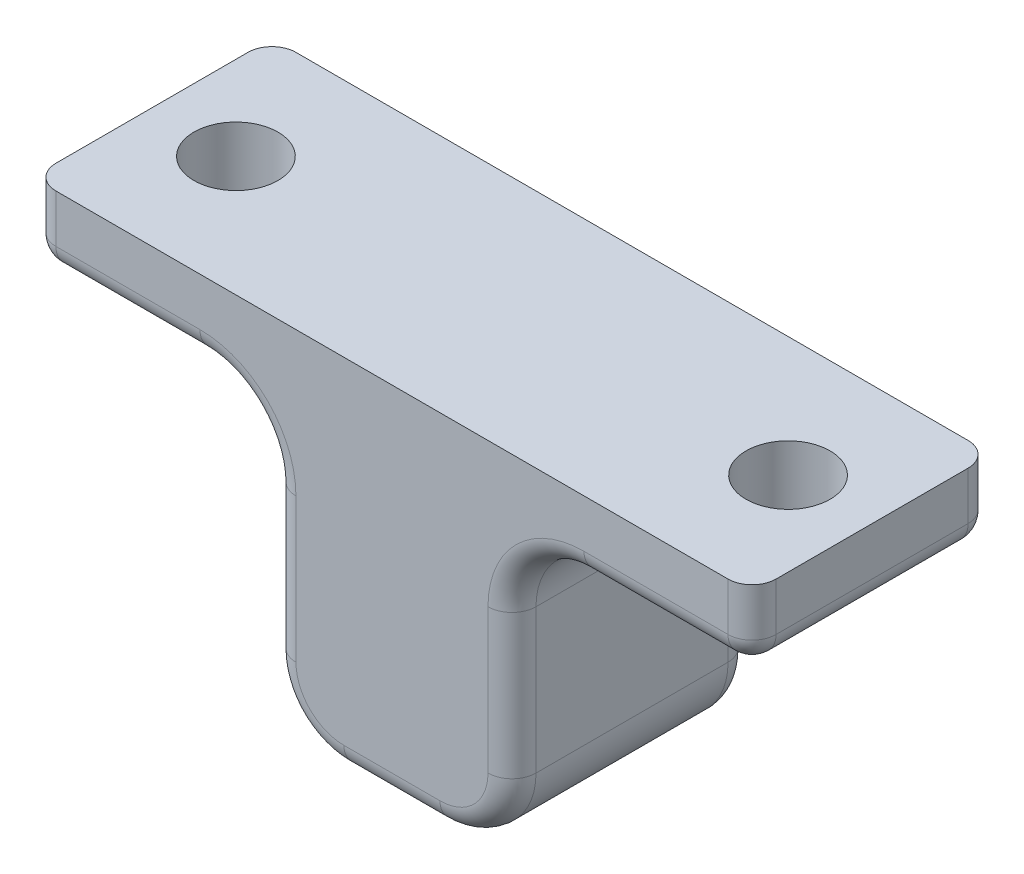
SolidWorks part; units mm, degrees
ref_plane "正面" through (0, 0, 0) normal (0, 0, 1) x (1, 0, 0)
ref_plane "平面" through (0, 0, 0) normal (0, 1, 0) x (1, 0, 0)
ref_plane "右側面" through (0, 0, 0) normal (1, 0, 0) x (0, 0, -1)
sketch "ｽｹｯﾁ1" plane through (0, 0, 0) normal (0, 0, 1) x (1, 0, 0)
  line L0 (0, 10) -> (0, -5)
  line L1 (5, -5) -> (-5, -5)
  line L2 (5, -5) -> (5, 10)
  line L3 (5, 10) -> (-5, 10)
  line L4 (-5, -5) -> (-5, 10)
  line L5 (5, 10) -> (15, 10)
  line L6 (5, 10) -> (5, 7)
  line L7 (5, 7) -> (15, 7)
  line L8 (15, 10) -> (15, 7)
  line L9 (-15, 10) -> (-15, 7)
  line L10 (-5, 7) -> (-15, 7)
  line L11 (-5, 10) -> (-5, 7)
  line L12 (-5, 10) -> (-15, 10)
  line L13 (5, -5) -> (5, 10)
  line L14 (-5, -5) -> (-5, 10)
  line L15 (5, 10) -> (15, 10)
  line L16 (15, 10) -> (5, 10)
  dimension "D1" = 15
  dimension "D2" = 10
  dimension "D5" = 3
  dimension "D6" = 10
extrude "ﾎﾞｽ - 押し出し1" add sketch "ｽｹｯﾁ1" along normal blind 10 contours L2 L3 L0 L1 | L8 L5 L2 L7 | L4 L1 L0 L3 | L4 L12 L9 L10
sketch "ｽｹｯﾁ2" plane through (0, 0, 0) normal (0, 0, -1) x (-1, 0, 0)
  circle A0 centre (0, 0) radius 3.2
  dimension "D1" = 6.4
extrude "ｶｯﾄ - 押し出し1" cut sketch "ｽｹｯﾁ2" against normal blind 8
sketch "ｽｹｯﾁ3" plane through (0, 7, 0) normal (0, -1, 0) x (1, 0, 0)
  line L0 (-15, 10) -> (-15, 0) construction
  line L1 (-5, 0) -> (-15, 0) construction
  line L2 (0, 0.3201) -> (0, 10.158)
  circle A0 centre (-11.5, 5) radius 1.75
  circle A1 centre (11.5, 5) radius 1.75
  dimension "D1" = 3.5
  dimension "D2" = 3.5
  dimension "D3" = 5
extrude "ｶｯﾄ - 押し出し2" cut sketch "ｽｹｯﾁ3" against normal through all contours A0 | A1
fillet "ﾌｨﾚｯﾄ1" radius 3 4 edges at (-5, 7, 5) (5, 7, 5) (-5, -5, 5) (5, -5, 5)
fillet "ﾌｨﾚｯﾄ2" radius 1 24 edges at (11.5, 7, 10) (11.5, 7, 0) (5.8787, 6.1213, 10) (5.8787, 6.1213, 0) (5, 1, 0) (5, 1, 10) (4.1213, -4.1213, 10) (4.1213, -4.1213, 0) (0, -5, 10) (0, -5, 0) (-4.1213, -4.1213, 10) (-4.1213, -4.1213, 0) (-5, 1, 10) (-5, 1, 0) (-5.8787, 6.1213, 10) (-5.8787, 6.1213, 0) (-15, 8.5, 0) (-15, 8.5, 10) (15, 8.5, 0) (15, 8.5, 10) (15, 7, 5) (-11.5, 7, 0) (-11.5, 7, 10) (-15, 7, 5)
